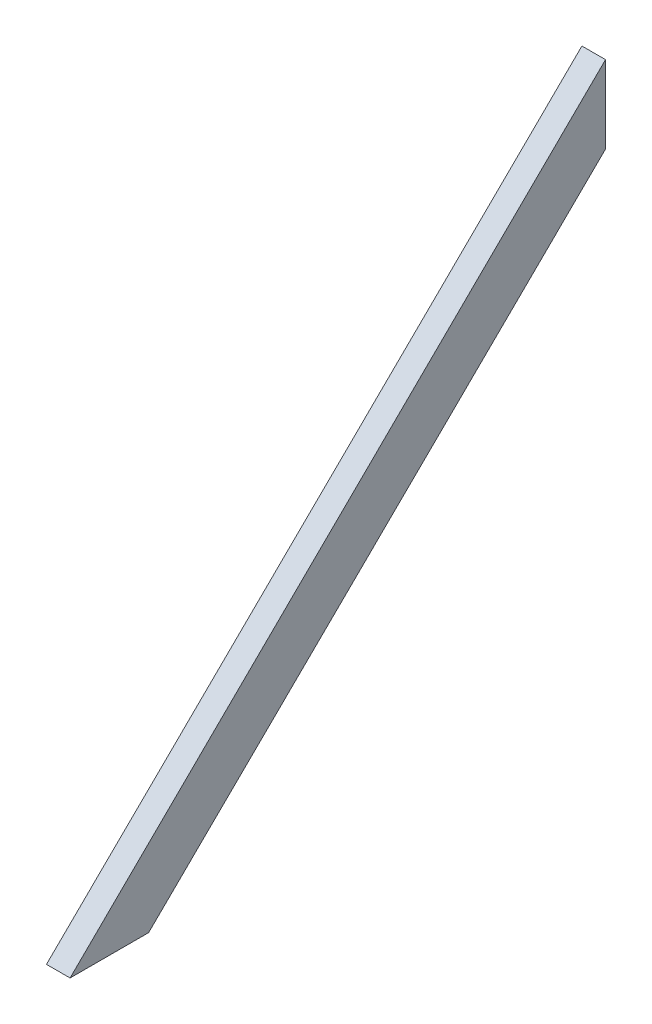
SolidWorks part; units mm, degrees
ref_plane "Front Plane" through (0, 0, 0) normal (0, 0, 1) x (1, 0, 0)
ref_plane "Top Plane" through (0, 0, 0) normal (0, 1, 0) x (1, 0, 0)
ref_plane "Right Plane" through (0, 0, 0) normal (1, 0, 0) x (0, 0, -1)
sketch "Sketch1" plane through (0, 0, 0) normal (1, 0, 0) x (0, 0, -1)
  line L0 (-431.8, -425.45) -> (-305.1347, -425.45)
  line L1 (-431.8, -425.45) -> (431.8, -425.45) construction
  line L2 (-431.8, -425.45) -> (-431.8, 425.45) construction
  line L3 (-431.8, 425.45) -> (431.8, 425.45) construction
  line L4 (431.8, -425.45) -> (431.8, 425.45) construction
  line L5 (-431.8, -425.45) -> (431.8, 425.45)
  line L6 (-431.8, 425.45) -> (431.8, -425.45) construction
  line L7 (-305.1347, -425.45) -> (431.8, 300.6474)
  line L8 (431.8, 300.6474) -> (431.8, 425.45)
  line L9 (-305.1347, -425.45) -> (-367.5291, -362.1243) construction
  line L10 (431.8, 300.6474) -> (369.4056, 363.9731) construction
  point P0 (0, 0)
  dimension "D1" = 850.9
  dimension "D2" = 863.6
  dimension "D3" = 88.9
  dimension "D4" = 1212.3678
  dimension "D5" = 87.5926
  dimension "D6" = 90.2269
extrude "Boss-Extrude1" add sketch "Sketch1" along normal blind 38.1 contours L5 L8 L7 L0
